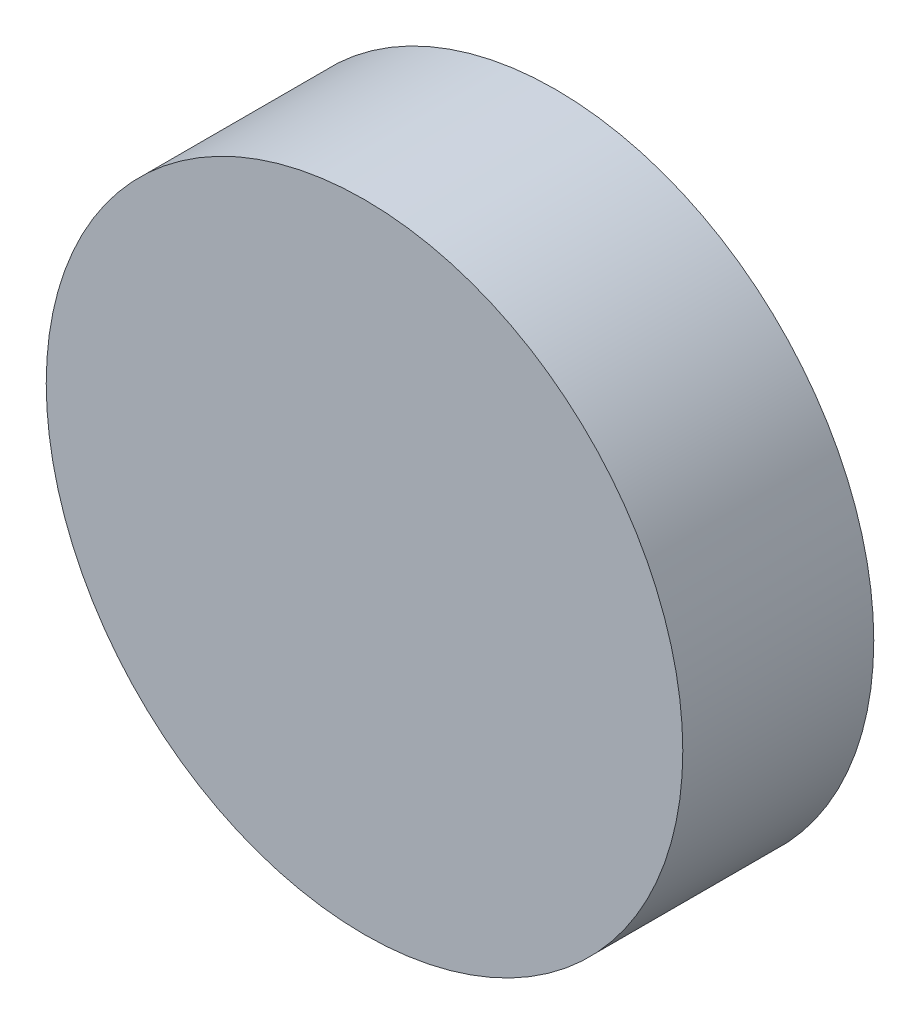
SolidWorks part; units mm, degrees
material "ABS PC"
ref_plane "Front Plane" through (0, 0, 0) normal (0, 0, 1) x (1, 0, 0)
ref_plane "Top Plane" through (0, 0, 0) normal (0, 1, 0) x (1, 0, 0)
ref_plane "Right Plane" through (0, 0, 0) normal (1, 0, 0) x (0, 0, -1)
sketch "Sketch1" plane through (0, 0, 0) normal (0, 0, 1) x (1, 0, 0)
  line L0 (2.2089, 3.5894) -> (-2.0041, 3.7077)
  line L1 (-2.572, -4.1795) -> (2.3335, -4.3172)
  line L2 (2.3335, -4.3172) -> (4.9055, -0.1377)
  line L3 (4.9055, -0.1377) -> (2.572, 4.1795)
  line L4 (2.572, 4.1795) -> (-2.3335, 4.3172)
  line L5 (-2.3335, 4.3172) -> (-4.9055, 0.1377)
  line L6 (-4.9055, 0.1377) -> (-2.572, -4.1795)
  line L7 (-2.0041, 3.7077) -> (-4.213, 0.1182)
  line L8 (-4.213, 0.1182) -> (-2.2089, -3.5894)
  line L9 (-2.2089, -3.5894) -> (2.0041, -3.7077)
  line L10 (2.0041, -3.7077) -> (4.213, -0.1182)
  line L11 (4.213, -0.1182) -> (2.2089, 3.5894)
  circle A0 centre (0, 0) radius 4.25 construction
  dimension "D1" = 8.5
  dimension "D2" = 0.6
extrude "Boss-Extrude1" add sketch "Sketch1" along normal blind 2
sketch "Sketch2" plane through (0, 0, 2) normal (0, 0, 1) x (1, 0, 0)
  circle A0 centre (0, 0) radius 10
  dimension "D1" = 20
extrude "Boss-Extrude2" add sketch "Sketch2" along normal blind 6
sketch "Sketch5" plane through (0, 0, 2) normal (0, 0, -1) x (-1, 0, 0)
  line L1 (-2.2089, 3.5894) -> (-4.213, -0.1182)
  line L2 (-4.213, -0.1182) -> (-2.0041, -3.7077)
  line L3 (-2.0041, -3.7077) -> (2.2089, -3.5894)
  line L4 (2.2089, -3.5894) -> (4.213, 0.1182)
  line L5 (4.213, 0.1182) -> (2.0041, 3.7077)
  line L6 (2.0041, 3.7077) -> (-2.2089, 3.5894)
  circle A0 centre (0, 0) radius 3.65 construction
extrude "Cut-Extrude1" cut sketch "Sketch5" against normal blind 2
